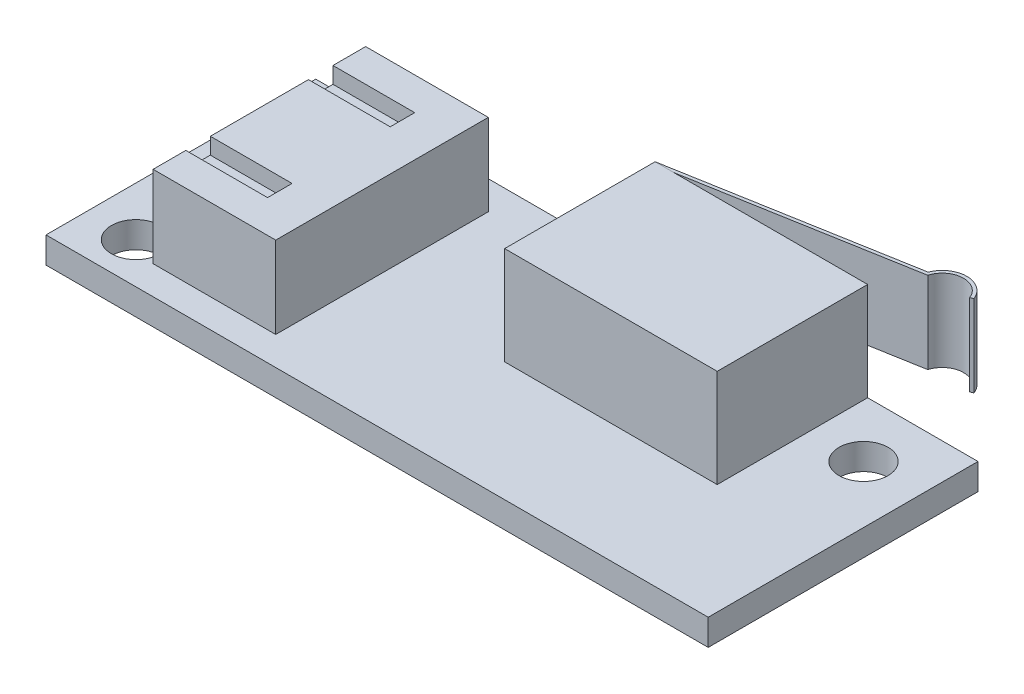
SolidWorks part; units mm, degrees
ref_plane "Front" through (0, 0, 0) normal (0, 0, 1) x (1, 0, 0)
ref_plane "Top" through (0, 0, 0) normal (0, 1, 0) x (1, 0, 0)
ref_plane "Right" through (0, 0, 0) normal (1, 0, 0) x (0, 0, -1)
sketch "Sketch1" plane through (0, 0, 0) normal (0, 1, 0) x (1, 0, 0)
  line L1 (-20.25, -8.25) -> (20.25, -8.25)
  line L2 (-20.25, -8.25) -> (-20.25, 8.25)
  line L3 (-20.25, 8.25) -> (20.25, 8.25)
  line L4 (20.25, -8.25) -> (20.25, 8.25)
  line L5 (-20.25, -8.25) -> (20.25, 8.25) construction
  line L6 (-20.25, 8.25) -> (20.25, -8.25) construction
  circle A0 centre (-17.25, -5.75) radius 1.5
  circle A1 centre (-17.25, 4.75) radius 1.5
  circle A2 centre (-2.25, 4.75) radius 1.5
  circle A3 centre (16.75, 4.75) radius 1.5
  point P0 (0, 0)
  dimension "D3" = 3
  dimension "D1" = 40.5
  dimension "D2" = 16.5
  dimension "D4" = 3
  dimension "D5" = 10.5
  dimension "D6" = 3.5
  dimension "D7" = 3.5
  dimension "D8" = 19
extrude "Boss-Extrude1" add sketch "Sketch1" along normal blind 1.6
sketch "Sketch2" plane through (0, 1.6, 0) normal (0, 1, 0) x (1, 0, 0)
  line L0 (20.25, 8.25) -> (-20.25, 8.25) construction
  line L1 (0.5, 8.25) -> (13.5, 8.25)
  line L2 (0.5, 8.25) -> (0.5, -0.95)
  line L3 (0.5, -0.95) -> (13.5, -0.95)
  line L4 (13.5, 8.25) -> (13.5, -0.95)
  line L5 (0.5, 8.25) -> (13.5, -0.95) construction
  line L6 (0.5, -0.95) -> (13.5, 8.25) construction
  line L7 (20.25, -8.25) -> (20.25, 8.25) construction
  point P0 (7, 3.65)
  dimension "D1" = 13
  dimension "D2" = 9.2
  dimension "D3" = 13.25
extrude "Boss-Extrude2" add sketch "Sketch2" along normal blind 6 separate body
sketch "Sketch3" plane through (0, 1.6, 0) normal (0, 1, 0) x (1, 0, 0)
  line L0 (-20.25, 8.25) -> (-20.25, -8.25) construction
  line L1 (-15.45, 6.5) -> (-7.95, 6.5)
  line L2 (-15.45, 6.5) -> (-15.45, -6.5)
  line L3 (-15.45, -6.5) -> (-7.95, -6.5)
  line L4 (-7.95, 6.5) -> (-7.95, -6.5)
  line L5 (-15.45, 6.5) -> (-7.95, -6.5) construction
  line L6 (-15.45, -6.5) -> (-7.95, 6.5) construction
  point P0 (-11.7, 0)
  dimension "D1" = 7.5
  dimension "D2" = 13
  dimension "D3" = 4.8
extrude "Boss-Extrude3" add sketch "Sketch3" along normal blind 5 separate body
sketch "Sketch4" plane through (0, 6.6, 0) normal (0, 1, 0) x (1, 0, 0)
  line L0 (-15.45, 6.5) -> (-15.45, -6.5) construction
  line L1 (-10.45, 4.5) -> (-15.45, 4.5)
  line L2 (-10.45, 4.5) -> (-10.45, 3)
  line L3 (-10.45, 3) -> (-15.45, 3)
  line L4 (-15.45, 4.5) -> (-15.45, 3)
  line L5 (-10.45, 4.5) -> (-15.45, 3) construction
  line L6 (-10.45, 3) -> (-15.45, 4.5) construction
  line L7 (-15.45, 0) -> (-7.95, 0) construction
  line L8 (-7.95, -6.5) -> (-7.95, 6.5) construction
  line L9 (-10.45, -4.5) -> (-10.45, -3)
  line L10 (-10.45, -3) -> (-15.45, -3)
  line L11 (-10.45, -4.5) -> (-15.45, -4.5)
  line L12 (-15.45, -4.5) -> (-15.45, -3)
  point P0 (-12.95, 3.75)
  dimension "D1" = 1.5
  dimension "D2" = 5
  dimension "D3" = 3
extrude "Cut-Extrude1" cut sketch "Sketch4" against normal blind 1
sketch "Sketch5" plane through (0, 7.6, 0) normal (0, 1, 0) x (1, 0, 0)
  line L0 (0.5, 8.25) -> (14.7, 10.7538)
  line L2 (13.5, 8.25) -> (0.5, 8.25) construction
  arc A0 (14.7, 10.7538) -> (17.5, 10.7538) centre (16.1, 10.2153) cw
  dimension "D2" = 1.5
  dimension "D1" = 10
  dimension "D3" = 17
  dimension "D4" = 2.8
extrude "Extrude-Thin1" add sketch "Sketch5" against normal blind 5 separate body thin
